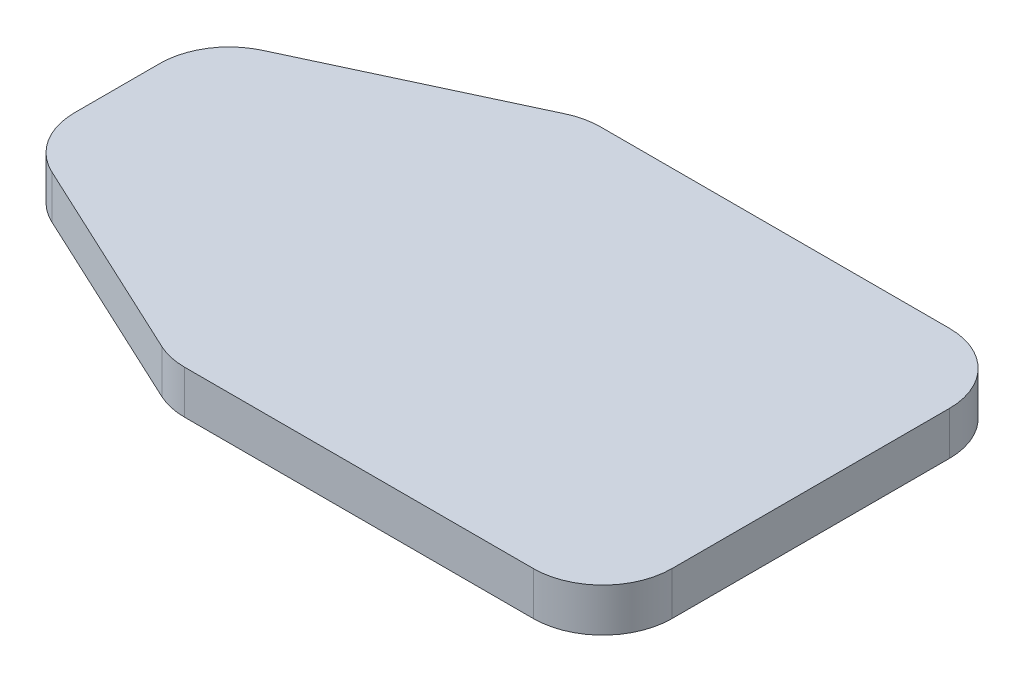
SolidWorks part; units mm, degrees
ref_plane "Front Plane" through (0, 0, 0) normal (0, 0, 1) x (1, 0, 0)
ref_plane "Top Plane" through (0, 0, 0) normal (0, 1, 0) x (1, 0, 0)
ref_plane "Right Plane" through (0, 0, 0) normal (1, 0, 0) x (0, 0, -1)
sketch "Sketch1" plane through (0, 0, 0) normal (0, 1, 0) x (1, 0, 0)
  line L0 (-25.4, 6.35) -> (-6.35, 15.24)
  line L1 (-25.4, 15.24) -> (25.4, 15.24)
  line L2 (-25.4, 15.24) -> (-25.4, -15.24)
  line L3 (-25.4, -15.24) -> (25.4, -15.24)
  line L4 (25.4, 15.24) -> (25.4, -15.24)
  line L5 (-25.4, -6.35) -> (-6.35, -15.24)
  point P4 (0, 15.24)
  point P5 (-25.4, 0)
  dimension "D1" = 30.48
  dimension "D2" = 50.8
  dimension "D3" = 19.05
  dimension "D4" = 8.89
extrude "Boss-Extrude1" add sketch "Sketch1" along normal blind 3.175 contours L2 L5 L3 L4 L1 L0
fillet "Fillet2" radius 5.08 6 edges at (25.4, 1.5875, 15.24) (25.4, 1.5875, -15.24) (-6.35, 1.5875, -15.24) (-25.4, 1.5875, -6.35) (-25.4, 1.5875, 6.35) (-6.35, 1.5875, 15.24)
